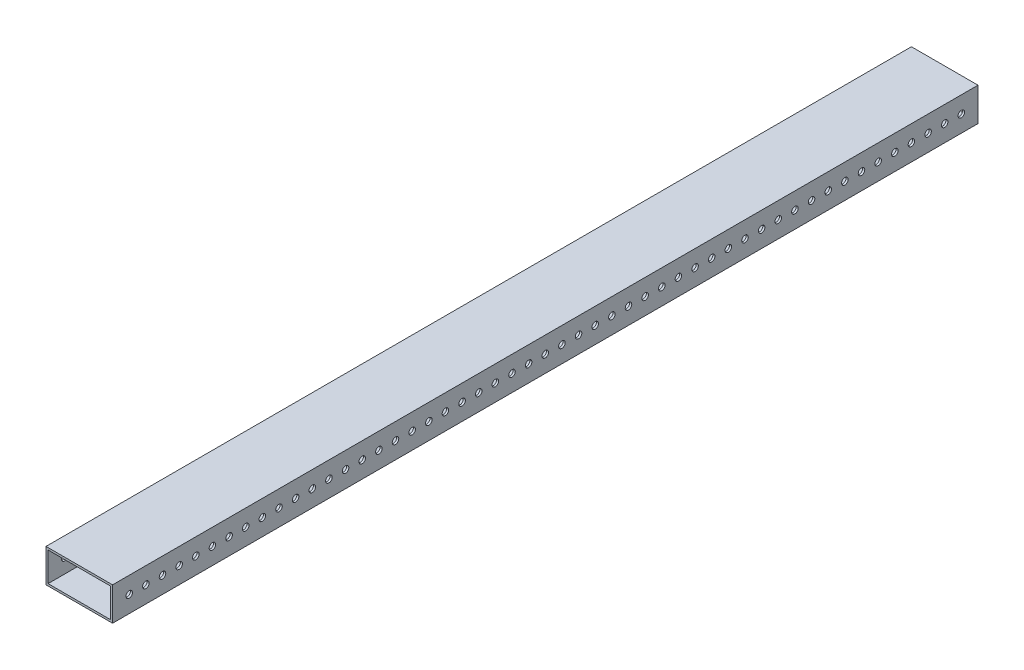
SolidWorks part; units mm, degrees
ref_plane "Front Plane" through (0, 0, 0) normal (0, 0, 1) x (1, 0, 0)
ref_plane "Top Plane" through (0, 0, 0) normal (0, 1, 0) x (1, 0, 0)
ref_plane "Right Plane" through (0, 0, 0) normal (1, 0, 0) x (0, 0, -1)
sketch "Sketch1" plane through (0, 0, 0) normal (0, 0, 1) x (1, 0, 0)
  line L0 (1.5875, 1.5875) -> (49.2125, 1.5875)
  line L1 (0, 0) -> (50.8, 0)
  line L2 (0, 0) -> (0, 25.4)
  line L3 (0, 25.4) -> (50.8, 25.4)
  line L4 (50.8, 0) -> (50.8, 25.4)
  line L5 (49.2125, 1.5875) -> (49.2125, 23.8125)
  line L6 (1.5875, 23.8125) -> (49.2125, 23.8125)
  line L7 (1.5875, 1.5875) -> (1.5875, 23.8125)
  dimension "D1" = 50.8
  dimension "D2" = 25.4
  dimension "D3" = 1.5875
extrude "Boss-Extrude1" add sketch "Sketch1" along normal blind 660.4
sketch "Sketch2" plane through (0, 0, 0) normal (-1, 0, 0) x (0, 0, 1)
  line L0 (0, 25.4) -> (0, 0) construction
  line L1 (12.7, 12.7) -> (25.4, 12.7) construction
  circle A0 centre (12.7, 12.7) radius 2.4892
  circle A1 centre (25.4, 12.7) radius 2.4892
  circle A2 centre (38.1, 12.7) radius 2.4892
  circle A3 centre (50.8, 12.7) radius 2.4892
  circle A4 centre (63.5, 12.7) radius 2.4892
  circle A5 centre (76.2, 12.7) radius 2.4892
  circle A6 centre (88.9, 12.7) radius 2.4892
  circle A7 centre (101.6, 12.7) radius 2.4892
  circle A8 centre (114.3, 12.7) radius 2.4892
  circle A9 centre (127, 12.7) radius 2.4892
  circle A10 centre (139.7, 12.7) radius 2.4892
  circle A11 centre (152.4, 12.7) radius 2.4892
  circle A12 centre (165.1, 12.7) radius 2.4892
  circle A13 centre (177.8, 12.7) radius 2.4892
  circle A14 centre (190.5, 12.7) radius 2.4892
  circle A15 centre (203.2, 12.7) radius 2.4892
  circle A16 centre (215.9, 12.7) radius 2.4892
  circle A17 centre (228.6, 12.7) radius 2.4892
  circle A18 centre (241.3, 12.7) radius 2.4892
  circle A19 centre (254, 12.7) radius 2.4892
  circle A20 centre (266.7, 12.7) radius 2.4892
  circle A21 centre (279.4, 12.7) radius 2.4892
  circle A22 centre (292.1, 12.7) radius 2.4892
  circle A23 centre (304.8, 12.7) radius 2.4892
  circle A24 centre (317.5, 12.7) radius 2.4892
  circle A25 centre (330.2, 12.7) radius 2.4892
  circle A26 centre (342.9, 12.7) radius 2.4892
  circle A27 centre (355.6, 12.7) radius 2.4892
  circle A28 centre (368.3, 12.7) radius 2.4892
  circle A29 centre (381, 12.7) radius 2.4892
  circle A30 centre (393.7, 12.7) radius 2.4892
  circle A31 centre (406.4, 12.7) radius 2.4892
  circle A32 centre (419.1, 12.7) radius 2.4892
  circle A33 centre (431.8, 12.7) radius 2.4892
  circle A34 centre (444.5, 12.7) radius 2.4892
  circle A35 centre (457.2, 12.7) radius 2.4892
  circle A36 centre (469.9, 12.7) radius 2.4892
  circle A37 centre (482.6, 12.7) radius 2.4892
  circle A38 centre (495.3, 12.7) radius 2.4892
  circle A39 centre (508, 12.7) radius 2.4892
  circle A40 centre (520.7, 12.7) radius 2.4892
  circle A41 centre (533.4, 12.7) radius 2.4892
  circle A42 centre (546.1, 12.7) radius 2.4892
  circle A43 centre (558.8, 12.7) radius 2.4892
  circle A44 centre (571.5, 12.7) radius 2.4892
  circle A45 centre (584.2, 12.7) radius 2.4892
  circle A46 centre (596.9, 12.7) radius 2.4892
  circle A47 centre (609.6, 12.7) radius 2.4892
  circle A48 centre (622.3, 12.7) radius 2.4892
  circle A49 centre (635, 12.7) radius 2.4892
  circle A50 centre (647.7, 12.7) radius 2.4892
  point P5 (0, 12.7)
  dimension "D1" = 4.9784
  dimension "D2" = 12.7
  dimension "D4" = 12.7
  dimension "D3" = 51
extrude "Cut-Extrude1" cut sketch "Sketch2" against normal through all
